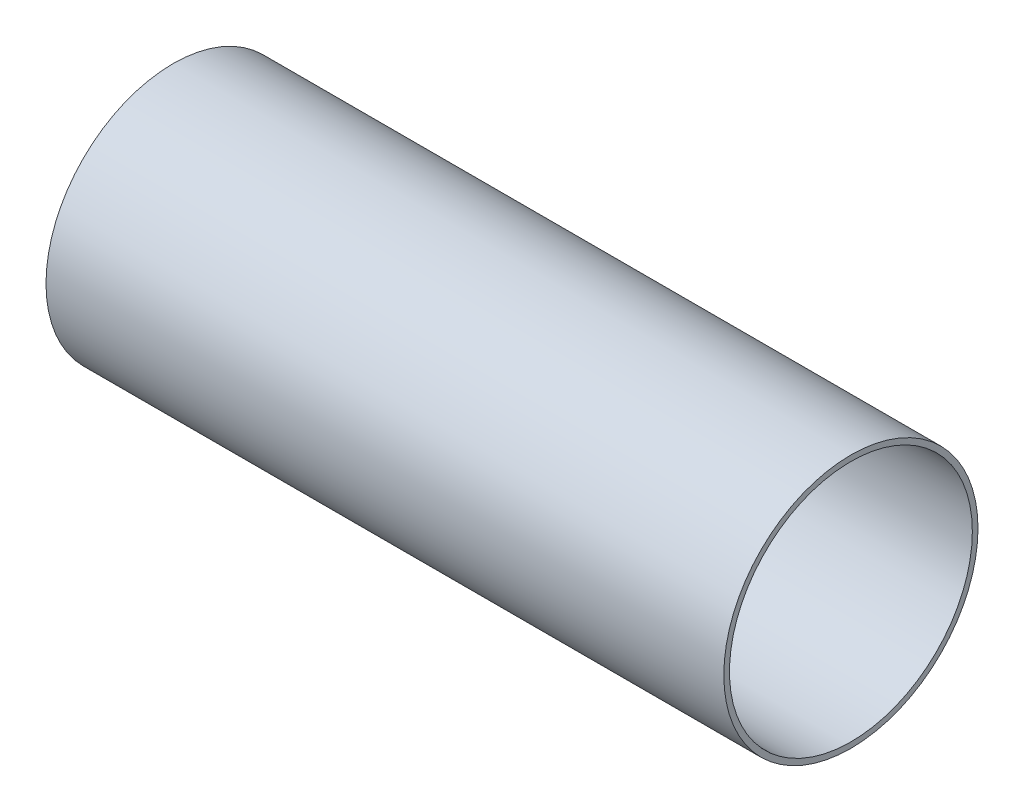
SolidWorks part; units mm, degrees
ref_plane "Front Plane" through (0, 0, 0) normal (0, 0, 1) x (1, 0, 0)
ref_plane "Top Plane" through (0, 0, 0) normal (0, 1, 0) x (1, 0, 0)
ref_plane "Right Plane" through (0, 0, 0) normal (1, 0, 0) x (0, 0, -1)
sketch "Sketch1" plane through (0, 0, 0) normal (1, 0, 0) x (0, 0, -1)
  circle A0 centre (0, 0) radius 571.5011
  circle A1 centre (0, 0) radius 546.1011
  dimension "OD" = 1143.0023
  dimension "Thickness" = 25.4001
extrude "Boss-Extrude1" add sketch "Sketch1" along normal mid plane 3048.0061
